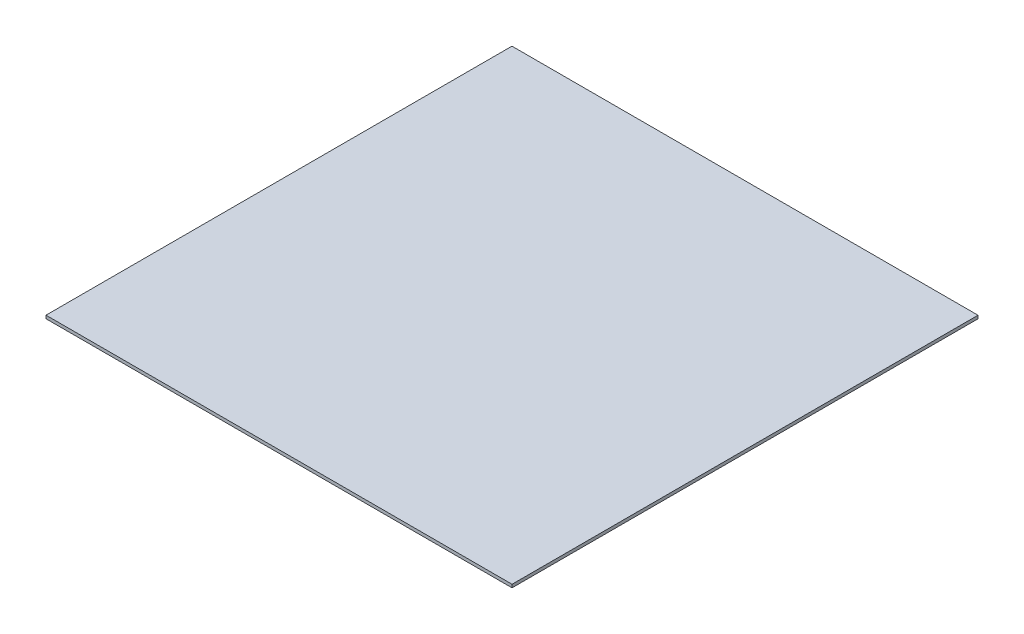
SolidWorks part; units mm, degrees
ref_plane "Front Plane" through (0, 0, 0) normal (0, 0, 1) x (1, 0, 0)
ref_plane "Top Plane" through (0, 0, 0) normal (0, 1, 0) x (1, 0, 0)
ref_plane "Right Plane" through (0, 0, 0) normal (1, 0, 0) x (0, 0, -1)
sketch "Sketch1" plane through (0, 0, 0) normal (0, 1, 0) x (1, 0, 0)
  line L1 (149.08, -149.05) -> (-149.08, -149.05)
  line L2 (149.08, -149.05) -> (149.08, 149.05)
  line L3 (149.08, 149.05) -> (-149.08, 149.05)
  line L4 (-149.08, -149.05) -> (-149.08, 149.05)
  line L5 (149.08, -149.05) -> (-149.08, 149.05) construction
  line L6 (149.08, 149.05) -> (-149.08, -149.05) construction
  point P0 (0, 0)
  dimension "D1" = 298.1
  dimension "D2" = 298.16
extrude "Boss-Extrude1" add sketch "Sketch1" along normal blind 2
